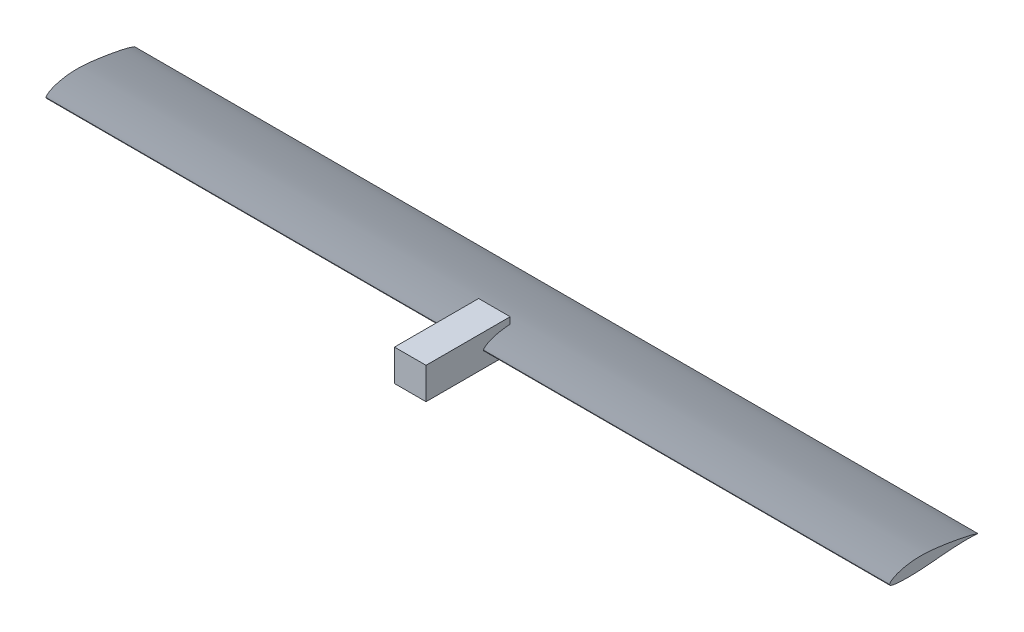
SolidWorks part; units mm, degrees
ref_plane "Front Plane" through (0, 0, 0) normal (0, 0, 1) x (1, 0, 0)
ref_plane "Top Plane" through (0, 0, 0) normal (0, 1, 0) x (1, 0, 0)
ref_plane "Right Plane" through (0, 0, 0) normal (1, 0, 0) x (0, 0, -1)
sketch "Sketch1" plane through (0, 0, 0) normal (0, 0, 1) x (1, 0, 0)
  line L1 (-38.1, -38.1) -> (38.1, -38.1)
  line L2 (-38.1, -38.1) -> (-38.1, 38.1)
  line L3 (-38.1, 38.1) -> (38.1, 38.1)
  line L4 (38.1, -38.1) -> (38.1, 38.1)
  line L5 (-38.1, -38.1) -> (38.1, 38.1) construction
  line L6 (-38.1, 38.1) -> (38.1, -38.1) construction
  point P0 (0, 0)
  dimension "D1" = 76.2
extrude "Boss-Extrude1" add sketch "Sketch1" along normal blind 203.2
ref_plane "Plane1" through (0, 0, 0) normal (1, 0, 0) x (0, 0, -1)
sketch "Sketch2" plane through (0, 0, 0) normal (1, 0, 0) x (0, 0, -1)
  line L0 (149.248, 0) -> (148.9527, 0.085)
  line L1 (148.9527, 0.085) -> (148.6318, 0.1805)
  line L2 (148.6318, 0.1805) -> (148.2889, 0.2852)
  line L3 (148.2889, 0.2852) -> (147.9274, 0.3978)
  line L4 (147.9274, 0.3978) -> (147.5509, 0.5172)
  line L5 (147.5509, 0.5172) -> (147.1628, 0.6419)
  line L6 (147.1628, 0.6419) -> (146.7668, 0.7709)
  line L7 (146.7668, 0.7709) -> (146.3662, 0.9027)
  line L8 (146.3662, 0.9027) -> (145.9638, 1.0365)
  line L9 (145.9638, 1.0365) -> (145.5586, 1.1722)
  line L10 (145.5586, 1.1722) -> (145.149, 1.3103)
  line L11 (145.149, 1.3103) -> (144.7332, 1.451)
  line L12 (144.7332, 1.451) -> (144.3094, 1.5947)
  line L13 (144.3094, 1.5947) -> (143.876, 1.7417)
  line L14 (143.876, 1.7417) -> (143.4313, 1.8924)
  line L15 (143.4313, 1.8924) -> (142.9734, 2.047)
  line L16 (142.9734, 2.047) -> (142.501, 2.2058)
  line L17 (142.501, 2.2058) -> (142.0139, 2.3686)
  line L18 (142.0139, 2.3686) -> (141.5119, 2.535)
  line L19 (141.5119, 2.535) -> (140.9953, 2.7047)
  line L20 (140.9953, 2.7047) -> (140.4639, 2.8774)
  line L21 (140.4639, 2.8774) -> (139.9179, 3.0526)
  line L22 (139.9179, 3.0526) -> (139.3573, 3.2301)
  line L23 (139.3573, 3.2301) -> (138.7822, 3.4095)
  line L24 (138.7822, 3.4095) -> (138.1925, 3.5905)
  line L25 (138.1925, 3.5905) -> (137.5882, 3.773)
  line L26 (137.5882, 3.773) -> (136.9692, 3.9568)
  line L27 (136.9692, 3.9568) -> (136.3354, 4.1419)
  line L28 (136.3354, 4.1419) -> (135.6868, 4.328)
  line L29 (135.6868, 4.328) -> (135.0233, 4.5152)
  line L30 (135.0233, 4.5152) -> (134.3449, 4.7033)
  line L31 (134.3449, 4.7033) -> (133.6513, 4.8921)
  line L32 (133.6513, 4.8921) -> (132.9427, 5.0817)
  line L33 (132.9427, 5.0817) -> (132.219, 5.2719)
  line L34 (132.219, 5.2719) -> (131.4803, 5.4629)
  line L35 (131.4803, 5.4629) -> (130.7267, 5.6547)
  line L36 (130.7267, 5.6547) -> (129.9582, 5.8474)
  line L37 (129.9582, 5.8474) -> (129.1749, 6.041)
  line L38 (129.1749, 6.041) -> (128.3769, 6.2355)
  line L39 (128.3769, 6.2355) -> (127.5642, 6.431)
  line L40 (127.5642, 6.431) -> (126.7369, 6.6275)
  line L41 (126.7369, 6.6275) -> (125.8952, 6.8251)
  line L42 (125.8952, 6.8251) -> (125.0394, 7.0237)
  line L43 (125.0394, 7.0237) -> (124.1695, 7.2233)
  line L44 (124.1695, 7.2233) -> (123.2858, 7.4239)
  line L45 (123.2858, 7.4239) -> (122.3885, 7.6256)
  line L46 (122.3885, 7.6256) -> (121.4778, 7.8282)
  line L47 (121.4778, 7.8282) -> (120.5538, 8.0319)
  line L48 (120.5538, 8.0319) -> (119.6168, 8.2366)
  line L49 (119.6168, 8.2366) -> (118.667, 8.4422)
  line L50 (118.667, 8.4422) -> (117.7046, 8.6487)
  line L51 (117.7046, 8.6487) -> (116.7298, 8.8561)
  line L52 (116.7298, 8.8561) -> (115.7427, 9.0643)
  line L53 (115.7427, 9.0643) -> (114.7437, 9.2733)
  line L54 (114.7437, 9.2733) -> (113.7328, 9.483)
  line L55 (113.7328, 9.483) -> (112.7104, 9.6934)
  line L56 (112.7104, 9.6934) -> (111.6766, 9.9044)
  line L57 (111.6766, 9.9044) -> (110.6316, 10.116)
  line L58 (110.6316, 10.116) -> (109.5756, 10.3281)
  line L59 (109.5756, 10.3281) -> (108.5089, 10.5407)
  line L60 (108.5089, 10.5407) -> (107.4316, 10.7537)
  line L61 (107.4316, 10.7537) -> (106.344, 10.9671)
  line L62 (106.344, 10.9671) -> (105.2463, 11.1808)
  line L63 (105.2463, 11.1808) -> (104.1387, 11.3947)
  line L64 (104.1387, 11.3947) -> (103.0214, 11.6089)
  line L65 (103.0214, 11.6089) -> (101.8947, 11.8232)
  line L66 (101.8947, 11.8232) -> (100.7587, 12.0375)
  line L67 (100.7587, 12.0375) -> (99.6137, 12.2519)
  line L68 (99.6137, 12.2519) -> (98.4599, 12.4662)
  line L69 (98.4599, 12.4662) -> (97.2975, 12.6804)
  line L70 (97.2975, 12.6804) -> (96.1269, 12.8944)
  line L71 (96.1269, 12.8944) -> (94.9481, 13.1082)
  line L72 (94.9481, 13.1082) -> (93.7614, 13.3217)
  line L73 (93.7614, 13.3217) -> (92.5671, 13.5348)
  line L74 (92.5671, 13.5348) -> (91.3654, 13.7475)
  line L75 (91.3654, 13.7475) -> (90.1565, 13.9597)
  line L76 (90.1565, 13.9597) -> (88.9408, 14.1713)
  line L77 (88.9408, 14.1713) -> (87.7183, 14.3823)
  line L78 (87.7183, 14.3823) -> (86.4894, 14.5926)
  line L79 (86.4894, 14.5926) -> (85.2544, 14.8021)
  line L80 (85.2544, 14.8021) -> (84.0133, 15.0108)
  line L81 (84.0133, 15.0108) -> (82.7666, 15.2186)
  line L82 (82.7666, 15.2186) -> (81.5144, 15.4254)
  line L83 (81.5144, 15.4254) -> (80.257, 15.6312)
  line L84 (80.257, 15.6312) -> (78.9947, 15.8358)
  line L85 (78.9947, 15.8358) -> (77.7276, 16.0393)
  line L86 (77.7276, 16.0393) -> (76.456, 16.2416)
  line L87 (76.456, 16.2416) -> (75.1801, 16.4426)
  line L88 (75.1801, 16.4426) -> (73.9002, 16.6421)
  line L89 (73.9002, 16.6421) -> (72.6166, 16.8403)
  line L90 (72.6166, 16.8403) -> (71.3295, 17.0368)
  line L91 (71.3295, 17.0368) -> (70.0391, 17.2318)
  line L92 (70.0391, 17.2318) -> (68.7457, 17.425)
  line L93 (68.7457, 17.425) -> (67.4496, 17.6163)
  line L94 (67.4496, 17.6163) -> (66.1509, 17.8058)
  line L95 (66.1509, 17.8058) -> (64.85, 17.9932)
  line L96 (64.85, 17.9932) -> (63.5471, 18.1785)
  line L97 (63.5471, 18.1785) -> (62.2424, 18.3617)
  line L98 (62.2424, 18.3617) -> (60.9363, 18.5426)
  line L99 (60.9363, 18.5426) -> (59.6289, 18.7211)
  line L100 (59.6289, 18.7211) -> (58.3205, 18.8972)
  line L101 (58.3205, 18.8972) -> (57.0114, 19.0708)
  line L102 (57.0114, 19.0708) -> (55.7018, 19.2419)
  line L103 (55.7018, 19.2419) -> (54.392, 19.4102)
  line L104 (54.392, 19.4102) -> (53.0822, 19.5759)
  line L105 (53.0822, 19.5759) -> (51.7727, 19.7386)
  line L106 (51.7727, 19.7386) -> (50.4638, 19.8984)
  line L107 (50.4638, 19.8984) -> (49.1557, 20.055)
  line L108 (49.1557, 20.055) -> (47.8486, 20.2084)
  line L109 (47.8486, 20.2084) -> (46.5428, 20.3584)
  line L110 (46.5428, 20.3584) -> (45.2385, 20.5049)
  line L111 (45.2385, 20.5049) -> (43.9361, 20.6477)
  line L112 (43.9361, 20.6477) -> (42.6358, 20.7868)
  line L113 (42.6358, 20.7868) -> (41.3377, 20.9219)
  line L114 (41.3377, 20.9219) -> (40.042, 21.0529)
  line L115 (40.042, 21.0529) -> (38.749, 21.1798)
  line L116 (38.749, 21.1798) -> (37.4588, 21.3022)
  line L117 (37.4588, 21.3022) -> (36.1715, 21.4201)
  line L118 (36.1715, 21.4201) -> (34.8875, 21.5334)
  line L119 (34.8875, 21.5334) -> (33.6068, 21.6418)
  line L120 (33.6068, 21.6418) -> (32.3296, 21.7453)
  line L121 (32.3296, 21.7453) -> (31.0561, 21.8436)
  line L122 (31.0561, 21.8436) -> (29.7863, 21.9368)
  line L123 (29.7863, 21.9368) -> (28.5204, 22.0247)
  line L124 (28.5204, 22.0247) -> (27.2584, 22.1073)
  line L125 (27.2584, 22.1073) -> (26.0006, 22.1844)
  line L126 (26.0006, 22.1844) -> (24.7469, 22.2558)
  line L127 (24.7469, 22.2558) -> (23.4976, 22.3216)
  line L128 (23.4976, 22.3216) -> (22.2526, 22.3817)
  line L129 (22.2526, 22.3817) -> (21.0122, 22.4359)
  line L130 (21.0122, 22.4359) -> (19.7765, 22.4842)
  line L131 (19.7765, 22.4842) -> (18.5454, 22.5266)
  line L132 (18.5454, 22.5266) -> (17.3193, 22.563)
  line L133 (17.3193, 22.563) -> (16.0982, 22.5934)
  line L134 (16.0982, 22.5934) -> (14.8821, 22.6177)
  line L135 (14.8821, 22.6177) -> (13.6713, 22.6359)
  line L136 (13.6713, 22.6359) -> (12.4659, 22.6479)
  line L137 (12.4659, 22.6479) -> (11.2658, 22.6537)
  line L138 (11.2658, 22.6537) -> (10.0713, 22.6534)
  line L139 (10.0713, 22.6534) -> (8.8825, 22.6468)
  line L140 (8.8825, 22.6468) -> (7.6994, 22.634)
  line L141 (7.6994, 22.634) -> (6.5221, 22.615)
  line L142 (6.5221, 22.615) -> (5.3507, 22.5897)
  line L143 (5.3507, 22.5897) -> (4.1853, 22.5582)
  line L144 (4.1853, 22.5582) -> (3.0261, 22.5205)
  line L145 (3.0261, 22.5205) -> (1.873, 22.4765)
  line L146 (1.873, 22.4765) -> (0.7263, 22.4263)
  line L147 (0.7263, 22.4263) -> (-0.414, 22.3699)
  line L148 (-0.414, 22.3699) -> (-1.5479, 22.3073)
  line L149 (-1.5479, 22.3073) -> (-2.6751, 22.2385)
  line L150 (-2.6751, 22.2385) -> (-3.7957, 22.1634)
  line L151 (-3.7957, 22.1634) -> (-4.9094, 22.0822)
  line L152 (-4.9094, 22.0822) -> (-6.0163, 21.9948)
  line L153 (-6.0163, 21.9948) -> (-7.1163, 21.9013)
  line L154 (-7.1163, 21.9013) -> (-8.2092, 21.8018)
  line L155 (-8.2092, 21.8018) -> (-9.295, 21.6962)
  line L156 (-9.295, 21.6962) -> (-10.3737, 21.5848)
  line L157 (-10.3737, 21.5848) -> (-11.4451, 21.4675)
  line L158 (-11.4451, 21.4675) -> (-12.5092, 21.3444)
  line L159 (-12.5092, 21.3444) -> (-13.566, 21.2157)
  line L160 (-13.566, 21.2157) -> (-14.6152, 21.0812)
  line L161 (-14.6152, 21.0812) -> (-15.657, 20.9413)
  line L162 (-15.657, 20.9413) -> (-16.691, 20.7959)
  line L163 (-16.691, 20.7959) -> (-17.7173, 20.6453)
  line L164 (-17.7173, 20.6453) -> (-18.7358, 20.4894)
  line L165 (-18.7358, 20.4894) -> (-19.7463, 20.3284)
  line L166 (-19.7463, 20.3284) -> (-20.7487, 20.1625)
  line L167 (-20.7487, 20.1625) -> (-21.7429, 19.9917)
  line L168 (-21.7429, 19.9917) -> (-22.7288, 19.8162)
  line L169 (-22.7288, 19.8162) -> (-23.7063, 19.6361)
  line L170 (-23.7063, 19.6361) -> (-24.6752, 19.4514)
  line L171 (-24.6752, 19.4514) -> (-25.6353, 19.2623)
  line L172 (-25.6353, 19.2623) -> (-26.5866, 19.069)
  line L173 (-26.5866, 19.069) -> (-27.5287, 18.8714)
  line L174 (-27.5287, 18.8714) -> (-28.4617, 18.6698)
  line L175 (-28.4617, 18.6698) -> (-29.3853, 18.4642)
  line L176 (-29.3853, 18.4642) -> (-30.2994, 18.2548)
  line L177 (-30.2994, 18.2548) -> (-31.2039, 18.0417)
  line L178 (-31.2039, 18.0417) -> (-32.0985, 17.8248)
  line L179 (-32.0985, 17.8248) -> (-32.9833, 17.6044)
  line L180 (-32.9833, 17.6044) -> (-33.858, 17.3804)
  line L181 (-33.858, 17.3804) -> (-34.7225, 17.1531)
  line L182 (-34.7225, 17.1531) -> (-35.5768, 16.9224)
  line L183 (-35.5768, 16.9224) -> (-36.4206, 16.6884)
  line L184 (-36.4206, 16.6884) -> (-37.2539, 16.4513)
  line L185 (-37.2539, 16.4513) -> (-38.0765, 16.2111)
  line L186 (-38.0765, 16.2111) -> (-38.8883, 15.9678)
  line L187 (-38.8883, 15.9678) -> (-39.6891, 15.7217)
  line L188 (-39.6891, 15.7217) -> (-40.4789, 15.4727)
  line L189 (-40.4789, 15.4727) -> (-41.2575, 15.2211)
  line L190 (-41.2575, 15.2211) -> (-42.0249, 14.9667)
  line L191 (-42.0249, 14.9667) -> (-42.7807, 14.7098)
  line L192 (-42.7807, 14.7098) -> (-43.5251, 14.4505)
  line L193 (-43.5251, 14.4505) -> (-44.2577, 14.1887)
  line L194 (-44.2577, 14.1887) -> (-44.9786, 13.9247)
  line L195 (-44.9786, 13.9247) -> (-45.6877, 13.6585)
  line L196 (-45.6877, 13.6585) -> (-46.3849, 13.3902)
  line L197 (-46.3849, 13.3902) -> (-47.0699, 13.1199)
  line L198 (-47.0699, 13.1199) -> (-47.7429, 12.8477)
  line L199 (-47.7429, 12.8477) -> (-48.4036, 12.5738)
  line L200 (-48.4036, 12.5738) -> (-49.052, 12.2981)
  line L201 (-49.052, 12.2981) -> (-49.688, 12.0208)
  line L202 (-49.688, 12.0208) -> (-50.3115, 11.742)
  line L203 (-50.3115, 11.742) -> (-50.9225, 11.4618)
  line L204 (-50.9225, 11.4618) -> (-51.5207, 11.1803)
  line L205 (-51.5207, 11.1803) -> (-52.1063, 10.8976)
  line L206 (-52.1063, 10.8976) -> (-52.679, 10.6138)
  line L207 (-52.679, 10.6138) -> (-53.2387, 10.329)
  line L208 (-53.2387, 10.329) -> (-53.7855, 10.0433)
  line L209 (-53.7855, 10.0433) -> (-54.3193, 9.7568)
  line L210 (-54.3193, 9.7568) -> (-54.8399, 9.4697)
  line L211 (-54.8399, 9.4697) -> (-55.3472, 9.182)
  line L212 (-55.3472, 9.182) -> (-55.8413, 8.8938)
  line L213 (-55.8413, 8.8938) -> (-56.3221, 8.6054)
  line L214 (-56.3221, 8.6054) -> (-56.7894, 8.3167)
  line L215 (-56.7894, 8.3167) -> (-57.2433, 8.028)
  line L216 (-57.2433, 8.028) -> (-57.6836, 7.7393)
  line L217 (-57.6836, 7.7393) -> (-58.1103, 7.4508)
  line L218 (-58.1103, 7.4508) -> (-58.5233, 7.1625)
  line L219 (-58.5233, 7.1625) -> (-58.9227, 6.8748)
  line L220 (-58.9227, 6.8748) -> (-59.3083, 6.5876)
  line L221 (-59.3083, 6.5876) -> (-59.6801, 6.3012)
  line L222 (-59.6801, 6.3012) -> (-60.0382, 6.0157)
  line L223 (-60.0382, 6.0157) -> (-60.3824, 5.7312)
  line L224 (-60.3824, 5.7312) -> (-60.7127, 5.4479)
  line L225 (-60.7127, 5.4479) -> (-61.029, 5.1659)
  line L226 (-61.029, 5.1659) -> (-61.3314, 4.8855)
  line L227 (-61.3314, 4.8855) -> (-61.6197, 4.6068)
  line L228 (-61.6197, 4.6068) -> (-61.894, 4.33)
  line L229 (-61.894, 4.33) -> (-62.1542, 4.0553)
  line L230 (-62.1542, 4.0553) -> (-62.4002, 3.7828)
  line L231 (-62.4002, 3.7828) -> (-62.6321, 3.5128)
  line L232 (-62.6321, 3.5128) -> (-62.8497, 3.2455)
  line L233 (-62.8497, 3.2455) -> (-63.053, 2.9812)
  line L234 (-63.053, 2.9812) -> (-63.2419, 2.7201)
  line L235 (-63.2419, 2.7201) -> (-63.4163, 2.4628)
  line L236 (-63.4163, 2.4628) -> (-63.5761, 2.2094)
  line L237 (-63.5761, 2.2094) -> (-63.7212, 1.9603)
  line L238 (-63.7212, 1.9603) -> (-63.8516, 1.7159)
  line L239 (-63.8516, 1.7159) -> (-63.9672, 1.4765)
  line L240 (-63.9672, 1.4765) -> (-64.0677, 1.2424)
  line L241 (-64.0677, 1.2424) -> (-64.1527, 1.0137)
  line L242 (-64.1527, 1.0137) -> (-64.2217, 0.7903)
  line L243 (-64.2217, 0.7903) -> (-64.274, 0.5723)
  line L244 (-64.274, 0.5723) -> (-64.309, 0.3597)
  line L245 (-64.309, 0.3597) -> (-64.3262, 0.1524)
  line L246 (-64.3262, 0.1524) -> (-64.3251, -0.0494)
  line L247 (-64.3251, -0.0494) -> (-64.305, -0.2459)
  line L248 (-64.305, -0.2459) -> (-64.2654, -0.437)
  line L249 (-64.2654, -0.437) -> (-64.2061, -0.623)
  line L250 (-64.2061, -0.623) -> (-64.127, -0.8045)
  line L251 (-64.127, -0.8045) -> (-64.0279, -0.9818)
  line L252 (-64.0279, -0.9818) -> (-63.9087, -1.1552)
  line L253 (-63.9087, -1.1552) -> (-63.7692, -1.3252)
  line L254 (-63.7692, -1.3252) -> (-63.6093, -1.4921)
  line L255 (-63.6093, -1.4921) -> (-63.4288, -1.6565)
  line L256 (-63.4288, -1.6565) -> (-63.2277, -1.8185)
  line L257 (-63.2277, -1.8185) -> (-63.0063, -1.9784)
  line L258 (-63.0063, -1.9784) -> (-62.765, -2.136)
  line L259 (-62.765, -2.136) -> (-62.5042, -2.2916)
  line L260 (-62.5042, -2.2916) -> (-62.2243, -2.4452)
  line L261 (-62.2243, -2.4452) -> (-61.9258, -2.5967)
  line L262 (-61.9258, -2.5967) -> (-61.6089, -2.7463)
  line L263 (-61.6089, -2.7463) -> (-61.2742, -2.8939)
  line L264 (-61.2742, -2.8939) -> (-60.922, -3.0397)
  line L265 (-60.922, -3.0397) -> (-60.5523, -3.1835)
  line L266 (-60.5523, -3.1835) -> (-60.1653, -3.3252)
  line L267 (-60.1653, -3.3252) -> (-59.761, -3.4648)
  line L268 (-59.761, -3.4648) -> (-59.3396, -3.6022)
  line L269 (-59.3396, -3.6022) -> (-58.901, -3.7372)
  line L270 (-58.901, -3.7372) -> (-58.4453, -3.8698)
  line L271 (-58.4453, -3.8698) -> (-57.9726, -3.9999)
  line L272 (-57.9726, -3.9999) -> (-57.483, -4.1274)
  line L273 (-57.483, -4.1274) -> (-56.9766, -4.2523)
  line L274 (-56.9766, -4.2523) -> (-56.4533, -4.3745)
  line L275 (-56.4533, -4.3745) -> (-55.9133, -4.494)
  line L276 (-55.9133, -4.494) -> (-55.3566, -4.6109)
  line L277 (-55.3566, -4.6109) -> (-54.7833, -4.7249)
  line L278 (-54.7833, -4.7249) -> (-54.1935, -4.8363)
  line L279 (-54.1935, -4.8363) -> (-53.5872, -4.9448)
  line L280 (-53.5872, -4.9448) -> (-52.9645, -5.0506)
  line L281 (-52.9645, -5.0506) -> (-52.3255, -5.1536)
  line L282 (-52.3255, -5.1536) -> (-51.6704, -5.2537)
  line L283 (-51.6704, -5.2537) -> (-50.9991, -5.351)
  line L284 (-50.9991, -5.351) -> (-50.3119, -5.4456)
  line L285 (-50.3119, -5.4456) -> (-49.6088, -5.5373)
  line L286 (-49.6088, -5.5373) -> (-48.8899, -5.6262)
  line L287 (-48.8899, -5.6262) -> (-48.1553, -5.7123)
  line L288 (-48.1553, -5.7123) -> (-47.4052, -5.7956)
  line L289 (-47.4052, -5.7956) -> (-46.6396, -5.8761)
  line L290 (-46.6396, -5.8761) -> (-45.8587, -5.9538)
  line L291 (-45.8587, -5.9538) -> (-45.0626, -6.0286)
  line L292 (-45.0626, -6.0286) -> (-44.2515, -6.1006)
  line L293 (-44.2515, -6.1006) -> (-43.4254, -6.1698)
  line L294 (-43.4254, -6.1698) -> (-42.5845, -6.2361)
  line L295 (-42.5845, -6.2361) -> (-41.7289, -6.2995)
  line L296 (-41.7289, -6.2995) -> (-40.8588, -6.3601)
  line L297 (-40.8588, -6.3601) -> (-39.9742, -6.4178)
  line L298 (-39.9742, -6.4178) -> (-39.0754, -6.4727)
  line L299 (-39.0754, -6.4727) -> (-38.1625, -6.5247)
  line L300 (-38.1625, -6.5247) -> (-37.2356, -6.5739)
  line L301 (-37.2356, -6.5739) -> (-36.295, -6.6203)
  line L302 (-36.295, -6.6203) -> (-35.3407, -6.6638)
  line L303 (-35.3407, -6.6638) -> (-34.3729, -6.7047)
  line L304 (-34.3729, -6.7047) -> (-33.3918, -6.7427)
  line L305 (-33.3918, -6.7427) -> (-32.3976, -6.778)
  line L306 (-32.3976, -6.778) -> (-31.3904, -6.8105)
  line L307 (-31.3904, -6.8105) -> (-30.3703, -6.8403)
  line L308 (-30.3703, -6.8403) -> (-29.3377, -6.8673)
  line L309 (-29.3377, -6.8673) -> (-28.2926, -6.8917)
  line L310 (-28.2926, -6.8917) -> (-27.2352, -6.9134)
  line L311 (-27.2352, -6.9134) -> (-26.1657, -6.9323)
  line L312 (-26.1657, -6.9323) -> (-25.0843, -6.9486)
  line L313 (-25.0843, -6.9486) -> (-23.9912, -6.9623)
  line L314 (-23.9912, -6.9623) -> (-22.8865, -6.9732)
  line L315 (-22.8865, -6.9732) -> (-21.7706, -6.9814)
  line L316 (-21.7706, -6.9814) -> (-20.6435, -6.9869)
  line L317 (-20.6435, -6.9869) -> (-19.5055, -6.9898)
  line L318 (-19.5055, -6.9898) -> (-18.3567, -6.9898)
  line L319 (-18.3567, -6.9898) -> (-17.1974, -6.9872)
  line L320 (-17.1974, -6.9872) -> (-16.0279, -6.9818)
  line L321 (-16.0279, -6.9818) -> (-14.8482, -6.9737)
  line L322 (-14.8482, -6.9737) -> (-13.6587, -6.9629)
  line L323 (-13.6587, -6.9629) -> (-12.4595, -6.9493)
  line L324 (-12.4595, -6.9493) -> (-11.2509, -6.9331)
  line L325 (-11.2509, -6.9331) -> (-10.0332, -6.9142)
  line L326 (-10.0332, -6.9142) -> (-8.8065, -6.8925)
  line L327 (-8.8065, -6.8925) -> (-7.5711, -6.8682)
  line L328 (-7.5711, -6.8682) -> (-6.3272, -6.8412)
  line L329 (-6.3272, -6.8412) -> (-5.075, -6.8115)
  line L330 (-5.075, -6.8115) -> (-3.8149, -6.7789)
  line L331 (-3.8149, -6.7789) -> (-2.547, -6.7435)
  line L332 (-2.547, -6.7435) -> (-1.2715, -6.7051)
  line L333 (-1.2715, -6.7051) -> (0.0112, -6.6638)
  line L334 (0.0112, -6.6638) -> (1.301, -6.6193)
  line L335 (1.301, -6.6193) -> (2.5976, -6.5717)
  line L336 (2.5976, -6.5717) -> (3.9008, -6.521)
  line L337 (3.9008, -6.521) -> (5.2105, -6.4668)
  line L338 (5.2105, -6.4668) -> (6.5266, -6.4092)
  line L339 (6.5266, -6.4092) -> (7.8489, -6.348)
  line L340 (7.8489, -6.348) -> (9.1773, -6.2831)
  line L341 (9.1773, -6.2831) -> (10.5118, -6.2143)
  line L342 (10.5118, -6.2143) -> (11.8523, -6.1416)
  line L343 (11.8523, -6.1416) -> (13.1985, -6.0647)
  line L344 (13.1985, -6.0647) -> (14.5505, -5.9836)
  line L345 (14.5505, -5.9836) -> (15.9082, -5.8984)
  line L346 (15.9082, -5.8984) -> (17.2717, -5.8091)
  line L347 (17.2717, -5.8091) -> (18.6409, -5.7159)
  line L348 (18.6409, -5.7159) -> (20.016, -5.6187)
  line L349 (20.016, -5.6187) -> (21.3969, -5.5177)
  line L350 (21.3969, -5.5177) -> (22.7837, -5.413)
  line L351 (22.7837, -5.413) -> (24.1764, -5.3047)
  line L352 (24.1764, -5.3047) -> (25.5749, -5.1929)
  line L353 (25.5749, -5.1929) -> (26.9792, -5.0778)
  line L354 (26.9792, -5.0778) -> (28.3891, -4.9597)
  line L355 (28.3891, -4.9597) -> (29.8044, -4.8389)
  line L356 (29.8044, -4.8389) -> (31.225, -4.7157)
  line L357 (31.225, -4.7157) -> (32.6508, -4.5903)
  line L358 (32.6508, -4.5903) -> (34.0814, -4.463)
  line L359 (34.0814, -4.463) -> (35.5169, -4.3341)
  line L360 (35.5169, -4.3341) -> (36.957, -4.2039)
  line L361 (36.957, -4.2039) -> (38.4015, -4.0725)
  line L362 (38.4015, -4.0725) -> (39.8499, -3.9402)
  line L363 (39.8499, -3.9402) -> (41.3019, -3.8072)
  line L364 (41.3019, -3.8072) -> (42.7573, -3.6737)
  line L365 (42.7573, -3.6737) -> (44.2157, -3.5398)
  line L366 (44.2157, -3.5398) -> (45.6767, -3.4058)
  line L367 (45.6767, -3.4058) -> (47.1401, -3.272)
  line L368 (47.1401, -3.272) -> (48.6054, -3.1384)
  line L369 (48.6054, -3.1384) -> (50.0725, -3.0052)
  line L370 (50.0725, -3.0052) -> (51.5408, -2.8726)
  line L371 (51.5408, -2.8726) -> (53.0102, -2.7406)
  line L372 (53.0102, -2.7406) -> (54.4802, -2.6094)
  line L373 (54.4802, -2.6094) -> (55.9505, -2.4791)
  line L374 (55.9505, -2.4791) -> (57.4208, -2.3498)
  line L375 (57.4208, -2.3498) -> (58.8908, -2.2216)
  line L376 (58.8908, -2.2216) -> (60.36, -2.0946)
  line L377 (60.36, -2.0946) -> (61.8282, -1.969)
  line L378 (61.8282, -1.969) -> (63.2949, -1.8448)
  line L379 (63.2949, -1.8448) -> (64.7599, -1.7221)
  line L380 (64.7599, -1.7221) -> (66.2228, -1.601)
  line L381 (66.2228, -1.601) -> (67.6832, -1.4817)
  line L382 (67.6832, -1.4817) -> (69.1407, -1.3641)
  line L383 (69.1407, -1.3641) -> (70.5951, -1.2485)
  line L384 (70.5951, -1.2485) -> (72.046, -1.1349)
  line L385 (72.046, -1.1349) -> (73.4929, -1.0233)
  line L386 (73.4929, -1.0233) -> (74.9357, -0.9139)
  line L387 (74.9357, -0.9139) -> (76.3739, -0.8066)
  line L388 (76.3739, -0.8066) -> (77.8072, -0.7016)
  line L389 (77.8072, -0.7016) -> (79.2354, -0.5988)
  line L390 (79.2354, -0.5988) -> (80.658, -0.4985)
  line L391 (80.658, -0.4985) -> (82.0747, -0.4005)
  line L392 (82.0747, -0.4005) -> (83.4851, -0.305)
  line L393 (83.4851, -0.305) -> (84.8891, -0.212)
  line L394 (84.8891, -0.212) -> (86.2861, -0.1216)
  line L395 (86.2861, -0.1216) -> (87.6759, -0.0338)
  line L396 (87.6759, -0.0338) -> (89.058, 0.0513)
  line L397 (89.058, 0.0513) -> (90.4323, 0.1338)
  line L398 (90.4323, 0.1338) -> (91.7982, 0.2135)
  line L399 (91.7982, 0.2135) -> (93.1555, 0.2904)
  line L400 (93.1555, 0.2904) -> (94.5038, 0.3645)
  line L401 (94.5038, 0.3645) -> (95.8428, 0.4357)
  line L402 (95.8428, 0.4357) -> (97.1722, 0.504)
  line L403 (97.1722, 0.504) -> (98.4916, 0.5695)
  line L404 (98.4916, 0.5695) -> (99.8008, 0.632)
  line L405 (99.8008, 0.632) -> (101.0993, 0.6916)
  line L406 (101.0993, 0.6916) -> (102.387, 0.7483)
  line L407 (102.387, 0.7483) -> (103.6634, 0.802)
  line L408 (103.6634, 0.802) -> (104.9282, 0.8528)
  line L409 (104.9282, 0.8528) -> (106.1812, 0.9006)
  line L410 (106.1812, 0.9006) -> (107.422, 0.9454)
  line L411 (107.422, 0.9454) -> (108.6503, 0.9872)
  line L412 (108.6503, 0.9872) -> (109.8658, 1.0261)
  line L413 (109.8658, 1.0261) -> (111.0682, 1.062)
  line L414 (111.0682, 1.062) -> (112.2571, 1.0949)
  line L415 (112.2571, 1.0949) -> (113.4323, 1.1249)
  line L416 (113.4323, 1.1249) -> (114.5934, 1.1518)
  line L417 (114.5934, 1.1518) -> (115.7402, 1.1759)
  line L418 (115.7402, 1.1759) -> (116.8722, 1.197)
  line L419 (116.8722, 1.197) -> (117.9894, 1.2152)
  line L420 (117.9894, 1.2152) -> (119.0912, 1.2305)
  line L421 (119.0912, 1.2305) -> (120.1775, 1.243)
  line L422 (120.1775, 1.243) -> (121.248, 1.2527)
  line L423 (121.248, 1.2527) -> (122.3022, 1.2595)
  line L424 (122.3022, 1.2595) -> (123.34, 1.2636)
  line L425 (123.34, 1.2636) -> (124.3611, 1.265)
  line L426 (124.3611, 1.265) -> (125.3651, 1.2637)
  line L427 (125.3651, 1.2637) -> (126.3517, 1.2596)
  line L428 (126.3517, 1.2596) -> (127.3208, 1.253)
  line L429 (127.3208, 1.253) -> (128.272, 1.2437)
  line L430 (128.272, 1.2437) -> (129.2051, 1.2319)
  line L431 (129.2051, 1.2319) -> (130.1196, 1.2175)
  line L432 (130.1196, 1.2175) -> (131.0154, 1.2006)
  line L433 (131.0154, 1.2006) -> (131.8923, 1.1814)
  line L434 (131.8923, 1.1814) -> (132.7498, 1.1598)
  line L435 (132.7498, 1.1598) -> (133.5877, 1.136)
  line L436 (133.5877, 1.136) -> (134.4059, 1.1102)
  line L437 (134.4059, 1.1102) -> (135.2039, 1.0824)
  line L438 (135.2039, 1.0824) -> (135.9815, 1.0527)
  line L439 (135.9815, 1.0527) -> (136.7384, 1.0212)
  line L440 (136.7384, 1.0212) -> (137.4744, 0.988)
  line L441 (137.4744, 0.988) -> (138.1893, 0.9534)
  line L442 (138.1893, 0.9534) -> (138.8827, 0.9174)
  line L443 (138.8827, 0.9174) -> (139.5547, 0.8801)
  line L444 (139.5547, 0.8801) -> (140.2048, 0.8418)
  line L445 (140.2048, 0.8418) -> (140.833, 0.8027)
  line L446 (140.833, 0.8027) -> (141.4389, 0.7627)
  line L447 (141.4389, 0.7627) -> (142.0225, 0.7222)
  line L448 (142.0225, 0.7222) -> (142.5838, 0.6813)
  line L449 (142.5838, 0.6813) -> (143.1247, 0.6397)
  line L450 (143.1247, 0.6397) -> (143.6472, 0.5976)
  line L451 (143.6472, 0.5976) -> (144.1537, 0.5547)
  line L452 (144.1537, 0.5547) -> (144.6462, 0.511)
  line L453 (144.6462, 0.511) -> (145.1269, 0.4664)
  line L454 (145.1269, 0.4664) -> (145.598, 0.4208)
  line L455 (145.598, 0.4208) -> (146.0616, 0.3741)
  line L456 (146.0616, 0.3741) -> (146.5188, 0.3263)
  line L457 (146.5188, 0.3263) -> (146.967, 0.2778)
  line L458 (146.967, 0.2778) -> (147.4021, 0.2291)
  line L459 (147.4021, 0.2291) -> (147.8203, 0.1806)
  line L460 (147.8203, 0.1806) -> (148.2179, 0.133)
  line L461 (148.2179, 0.133) -> (148.591, 0.0867)
  line L462 (148.591, 0.0867) -> (148.9356, 0.0422)
  line L463 (148.9356, 0.0422) -> (149.248, 0)
  point P0 (0, 0)
extrude "Boss-Extrude2" add sketch "Sketch2" along normal blind 1018.36 and the other way blind 1018.36
